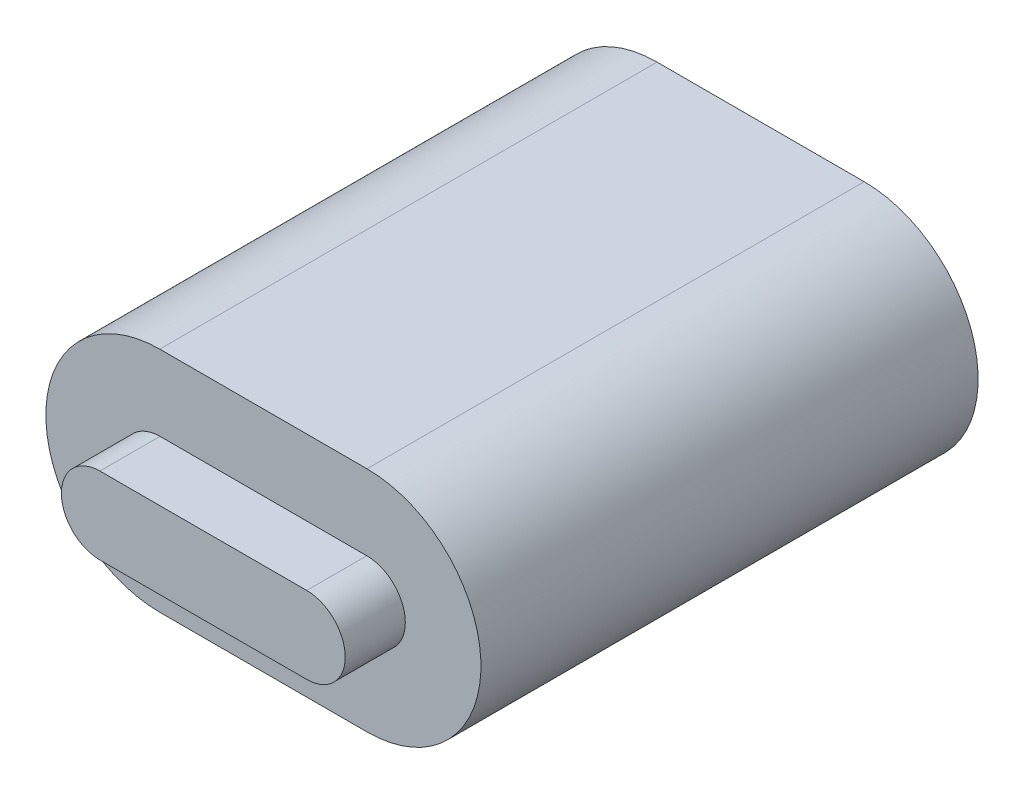
SolidWorks part; units mm, degrees
ref_plane "Front Plane" through (0, 0, 0) normal (0, 0, 1) x (1, 0, 0)
ref_plane "Top Plane" through (0, 0, 0) normal (0, 1, 0) x (1, 0, 0)
ref_plane "Right Plane" through (0, 0, 0) normal (1, 0, 0) x (0, 0, -1)
sketch "Sketch1" plane through (0, 0, 0) normal (0, 0, 1) x (1, 0, 0)
  line L0 (-2.495, 0) -> (2.495, 0) construction
  line L1 (-2.495, 0.93) -> (2.495, 0.93)
  line L2 (-2.495, -0.93) -> (2.495, -0.93)
  line L3 (-3.425, -1000) -> (-3.425, 49000) construction
  line L4 (3.425, -1000) -> (3.425, 49000) construction
  arc A0 (-2.495, 0.93) -> (-2.495, -0.93) centre (-2.495, 0) ccw
  arc A1 (2.495, -0.93) -> (2.495, 0.93) centre (2.495, 0) ccw
  point P2 (0, 0)
  point P11 (-3.425, 0)
  point P14 (3.425, 0)
  dimension "D1" = 1.86
  dimension "D2" = 6.85
extrude "Boss-Extrude1" add sketch "Sketch1" along normal blind 1.45
sketch "Sketch2" plane through (0, 0, 0) normal (0, 0, -1) x (-1, 0, 0)
  line L0 (-2.5, 0) -> (2.5, 0) construction
  line L1 (-2.5, 2.75) -> (2.5, 2.75)
  line L2 (-2.5, -2.75) -> (2.5, -2.75)
  line L3 (-5.25, -1000) -> (-5.25, 49000) construction
  line L4 (5.25, -1000) -> (5.25, 49000) construction
  arc A0 (-2.5, 2.75) -> (-2.5, -2.75) centre (-2.5, 0) ccw
  arc A1 (2.5, -2.75) -> (2.5, 2.75) centre (2.5, 0) ccw
  point P3 (0, 0)
  point P11 (-5.25, 0)
  point P14 (5.25, 0)
  dimension "D1" = 5.5
  dimension "D2" = 10.5
extrude "Boss-Extrude2" add sketch "Sketch2" along normal blind 12
